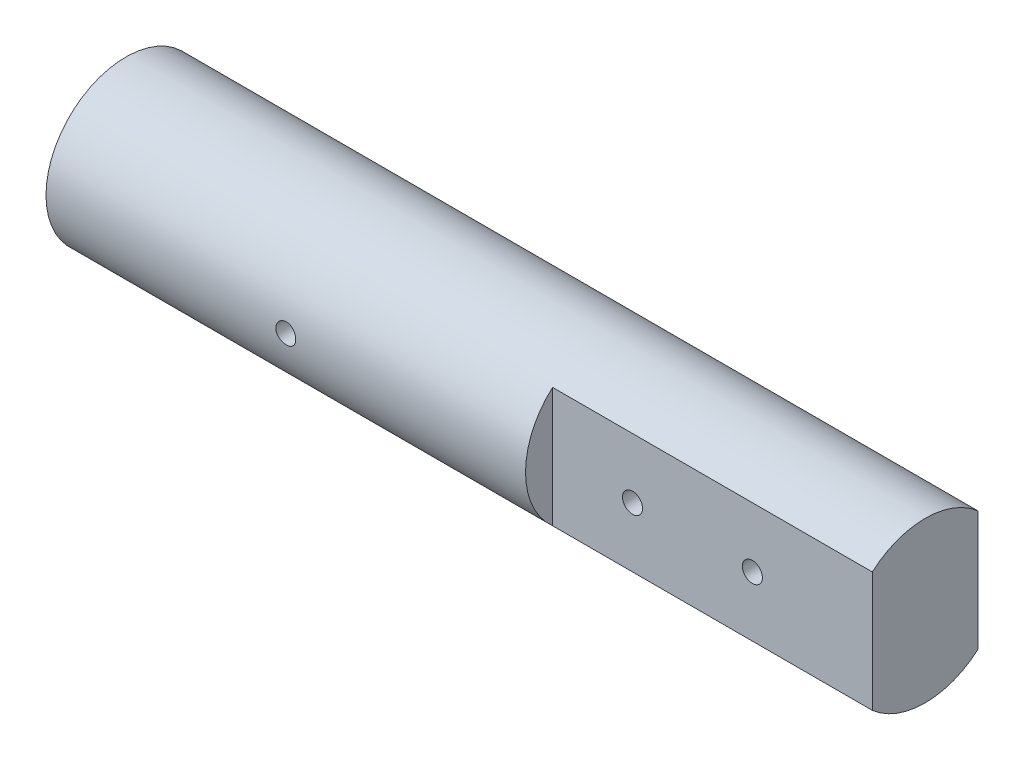
SolidWorks part; units mm, degrees
material "6061 Alloy"
ref_plane "Front Plane" through (0, 0, 0) normal (0, 0, 1) x (1, 0, 0)
ref_plane "Top Plane" through (0, 0, 0) normal (0, 1, 0) x (1, 0, 0)
ref_plane "Right Plane" through (0, 0, 0) normal (1, 0, 0) x (0, 0, -1)
sketch "Sketch1" plane through (0, 0, 0) normal (0, 0, 1) x (1, 0, 0)
  line L0 (0, 0) -> (0, 10)
  line L1 (0, 10) -> (60, 10)
  line L6 (60, 10) -> (60, 0)
  line L8 (0, 0) -> (60, 0)
  line L9 (0, 0) -> (60, 0) construction
  dimension "D2" = 60
  dimension "D3" = 20
revolve "Revolve1" add sketch "Sketch1" angle 360 about L8
sketch "Sketch3" plane through (60, 0, 0) normal (1, 0, 0) x (0, 0, -1)
  line L0 (-6.6144, -7.5) -> (-6.6144, 7.5)
  line L1 (6.6144, -7.5) -> (6.6144, 7.5)
  arc A1 (-6.6144, -7.5) -> (6.6144, -7.5) centre (0, 0) ccw
  arc A2 (6.6144, 7.5) -> (-6.6144, 7.5) centre (0, 0) ccw
  circle A3 centre (0, 0) radius 10 construction
  dimension "D1" = 15
extrude "Boss-Extrude1" add sketch "Sketch3" along normal blind 40
ref_plane "Plane1" through (0, 0, 10) normal (0, 0, 1) x (1, 0, 0)
hole_wizard "M3x0.5 Tapped Hole3" positions "Sketch6" profile "Sketch5" tap size "M3x0.5" standard "ANSI Metric"
sketch "Sketch6" plane through (0, 0, 10) normal (0, 0, 1) x (1, 0, 0)
  line L0 (0, 0) -> (60, 0) construction
  point P0 (30, 0)
  point P6 (30, 0)
sketch "Sketch5" plane through (30, 0, 10) normal (1, 0, 0) x (0, -1, 0)
  line L0 (0, 0) -> (0, 10.7511)
  line L1 (0, 10.7511) -> (1.25, 10)
  line L2 (1.25, 10) -> (1.25, 0)
  line L5 (1.25, 0) -> (0, 0)
  line L10 (0, 10.7511) -> (-1.25, 10) construction
  line L11 (0, -6.35) -> (0, 107.95) construction
  dimension "Tap Drill Dia." = 2.5
  dimension "Tap Drill Depth" = 10
  dimension "Drill Angle" = 118
cosmetic thread "Hole Thread6" parameters "D1"=6, "D2"=3
hole_wizard "M3x0.5 Tapped Hole2" positions "3DSketch2" profile "Sketch4" tap size "M3x0.5" standard "ANSI Metric"
sketch3d "3DSketch2"
  line L0 (100, 7.5, 6.6144) -> (100, -7.5, 6.6144) construction
  line L1 (60, 7.5, 6.6144) -> (60, -7.5, 6.6144) construction
  point P0 (70, 0, 6.6144)
  point P2 (85, 0, 6.6144)
  point P7 (100, 0, 6.6144)
  point P8 (85, 0, -6.6144)
  point P10 (70, 0, -6.6144)
  dimension "D1" = 10
  dimension "D2" = 15
sketch "Sketch4" plane through (70, 0, 6.6144) normal (1, 0, 0) x (0, -1, 0)
  line L0 (0, 0) -> (0, 5.7511)
  line L1 (0, 5.7511) -> (1.25, 5)
  line L2 (1.25, 5) -> (1.25, 0)
  line L5 (1.25, 0) -> (0, 0)
  line L10 (0, 5.7511) -> (-1.25, 5) construction
  line L11 (0, -6.35) -> (0, 107.95) construction
  dimension "Tap Drill Dia." = 2.5
  dimension "Tap Drill Depth" = 5
  dimension "Drill Angle" = 118
cosmetic thread "Hole Thread2" parameters "D1"=6, "D2"=3
cosmetic thread "Hole Thread3" parameters "D1"=6, "D2"=3
cosmetic thread "Hole Thread4" parameters "D1"=6, "D2"=3
cosmetic thread "Hole Thread5" parameters "D1"=6, "D2"=3
